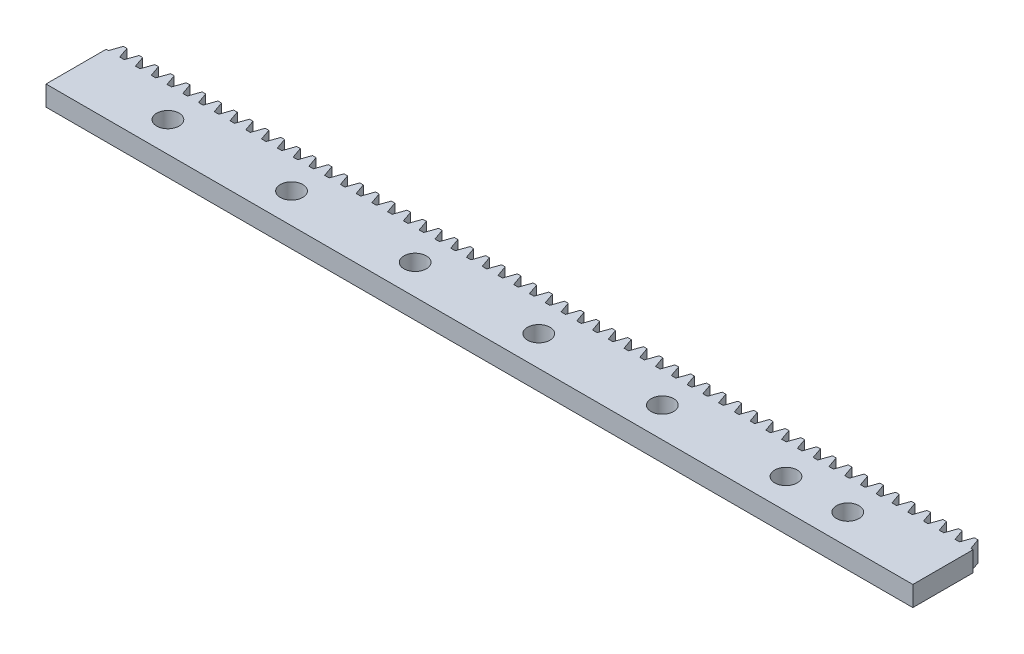
SolidWorks part; units mm, degrees
ref_plane "Front Plane" through (0, 0, 0) normal (0, 0, 1) x (1, 0, 0)
ref_plane "Top Plane" through (0, 0, 0) normal (0, 1, 0) x (1, 0, 0)
ref_plane "Right Plane" through (0, 0, 0) normal (1, 0, 0) x (0, 0, -1)
ref_plane "Plane1" through (0, 0, 0) normal (0, -1, 0) x (1, 0, 0)
sketch "Sketch1" plane through (0, 0, 0) normal (0, -1, 0) x (1, 0, 0)
  line L0 (14.6068, -4.7625) -> (15.3169, -4.7625)
  line L1 (15.3169, -4.7625) -> (15.9263, -6.5115)
  line L2 (15.9263, -6.5115) -> (16.491, -6.5115)
  line L3 (16.491, -6.5115) -> (17.1004, -4.7625)
  line L4 (12.1131, -4.7625) -> (12.8232, -4.7625)
  line L5 (12.8232, -4.7625) -> (13.4327, -6.5115)
  line L6 (13.4327, -6.5115) -> (13.9974, -6.5115)
  line L7 (13.9974, -6.5115) -> (14.6068, -4.7625)
  line L8 (9.6195, -4.7625) -> (10.3296, -4.7625)
  line L9 (10.3296, -4.7625) -> (10.939, -6.5115)
  line L10 (10.939, -6.5115) -> (11.5037, -6.5115)
  line L11 (11.5037, -6.5115) -> (12.1131, -4.7625)
  line L12 (7.1259, -4.7625) -> (7.836, -4.7625)
  line L13 (7.836, -4.7625) -> (8.4454, -6.5115)
  line L14 (8.4454, -6.5115) -> (9.0101, -6.5115)
  line L15 (9.0101, -6.5115) -> (9.6195, -4.7625)
  line L16 (4.6322, -4.7625) -> (5.3423, -4.7625)
  line L17 (5.3423, -4.7625) -> (5.9517, -6.5115)
  line L18 (5.9517, -6.5115) -> (6.5165, -6.5115)
  line L19 (6.5165, -6.5115) -> (7.1259, -4.7625)
  line L20 (2.1386, -4.7625) -> (2.8487, -4.7625)
  line L21 (2.8487, -4.7625) -> (3.4581, -6.5115)
  line L22 (3.4581, -6.5115) -> (4.0228, -6.5115)
  line L23 (4.0228, -6.5115) -> (4.6322, -4.7625)
  line L24 (-0.355, -4.7625) -> (0.355, -4.7625)
  line L25 (0.355, -4.7625) -> (0.9645, -6.5115)
  line L26 (0.9645, -6.5115) -> (1.5292, -6.5115)
  line L27 (1.5292, -6.5115) -> (2.1386, -4.7625)
  line L28 (-2.8487, -4.7625) -> (-2.1386, -4.7625)
  line L29 (-2.1386, -4.7625) -> (-1.5292, -6.5115)
  line L30 (-1.5292, -6.5115) -> (-0.9645, -6.5115)
  line L31 (-0.9645, -6.5115) -> (-0.355, -4.7625)
  line L32 (-5.3423, -4.7625) -> (-4.6322, -4.7625)
  line L33 (-4.6322, -4.7625) -> (-4.0228, -6.5115)
  line L34 (-4.0228, -6.5115) -> (-3.4581, -6.5115)
  line L35 (-3.4581, -6.5115) -> (-2.8487, -4.7625)
  line L36 (-7.836, -4.7625) -> (-7.1259, -4.7625)
  line L37 (-7.1259, -4.7625) -> (-6.5165, -6.5115)
  line L38 (-6.5165, -6.5115) -> (-5.9517, -6.5115)
  line L39 (-5.9517, -6.5115) -> (-5.3423, -4.7625)
  line L40 (-10.3296, -4.7625) -> (-9.6195, -4.7625)
  line L41 (-9.6195, -4.7625) -> (-9.0101, -6.5115)
  line L42 (-9.0101, -6.5115) -> (-8.4454, -6.5115)
  line L43 (-8.4454, -6.5115) -> (-7.836, -4.7625)
  line L44 (-12.8232, -4.7625) -> (-12.1131, -4.7625)
  line L45 (-12.1131, -4.7625) -> (-11.5037, -6.5115)
  line L46 (-11.5037, -6.5115) -> (-10.939, -6.5115)
  line L47 (-10.939, -6.5115) -> (-10.3296, -4.7625)
  line L48 (-15.3169, -4.7625) -> (-14.6068, -4.7625)
  line L49 (-14.6068, -4.7625) -> (-13.9974, -6.5115)
  line L50 (-13.9974, -6.5115) -> (-13.4327, -6.5115)
  line L51 (-13.4327, -6.5115) -> (-12.8232, -4.7625)
  line L52 (-17.8105, -4.7625) -> (-17.1004, -4.7625)
  line L53 (-17.1004, -4.7625) -> (-16.491, -6.5115)
  line L54 (-16.491, -6.5115) -> (-15.9263, -6.5115)
  line L55 (-15.9263, -6.5115) -> (-15.3169, -4.7625)
  line L56 (-20.3042, -4.7625) -> (-19.5941, -4.7625)
  line L57 (-19.5941, -4.7625) -> (-18.9846, -6.5115)
  line L58 (-18.9846, -6.5115) -> (-18.4199, -6.5115)
  line L59 (-18.4199, -6.5115) -> (-17.8105, -4.7625)
  line L60 (-22.7978, -4.7625) -> (-22.0877, -4.7625)
  line L61 (-22.0877, -4.7625) -> (-21.4783, -6.5115)
  line L62 (-21.4783, -6.5115) -> (-20.9136, -6.5115)
  line L63 (-20.9136, -6.5115) -> (-20.3042, -4.7625)
  line L64 (-25.2914, -4.7625) -> (-24.5813, -4.7625)
  line L65 (-24.5813, -4.7625) -> (-23.9719, -6.5115)
  line L66 (-23.9719, -6.5115) -> (-23.4072, -6.5115)
  line L67 (-23.4072, -6.5115) -> (-22.7978, -4.7625)
  line L68 (-27.7851, -4.7625) -> (-27.075, -4.7625)
  line L69 (-27.075, -4.7625) -> (-26.4656, -6.5115)
  line L70 (-26.4656, -6.5115) -> (-25.9009, -6.5115)
  line L71 (-25.9009, -6.5115) -> (-25.2914, -4.7625)
  line L72 (-30.2787, -4.7625) -> (-29.5686, -4.7625)
  line L73 (-29.5686, -4.7625) -> (-28.9592, -6.5115)
  line L74 (-28.9592, -6.5115) -> (-28.3945, -6.5115)
  line L75 (-28.3945, -6.5115) -> (-27.7851, -4.7625)
  line L76 (-32.7724, -4.7625) -> (-32.0623, -4.7625)
  line L77 (-32.0623, -4.7625) -> (-31.4528, -6.5115)
  line L78 (-31.4528, -6.5115) -> (-30.8881, -6.5115)
  line L79 (-30.8881, -6.5115) -> (-30.2787, -4.7625)
  line L80 (-35.266, -4.7625) -> (-34.5559, -4.7625)
  line L81 (-34.5559, -4.7625) -> (-33.9465, -6.5115)
  line L82 (-33.9465, -6.5115) -> (-33.3818, -6.5115)
  line L83 (-33.3818, -6.5115) -> (-32.7724, -4.7625)
  line L84 (-37.7596, -4.7625) -> (-37.0495, -4.7625)
  line L85 (-37.0495, -4.7625) -> (-36.4401, -6.5115)
  line L86 (-36.4401, -6.5115) -> (-35.8754, -6.5115)
  line L87 (-35.8754, -6.5115) -> (-35.266, -4.7625)
  line L88 (-40.2533, -4.7625) -> (-39.5432, -4.7625)
  line L89 (-39.5432, -4.7625) -> (-38.9338, -6.5115)
  line L90 (-38.9338, -6.5115) -> (-38.3691, -6.5115)
  line L91 (-38.3691, -6.5115) -> (-37.7596, -4.7625)
  line L92 (-42.7469, -4.7625) -> (-42.0368, -4.7625)
  line L93 (-42.0368, -4.7625) -> (-41.4274, -6.5115)
  line L94 (-41.4274, -6.5115) -> (-40.8627, -6.5115)
  line L95 (-40.8627, -6.5115) -> (-40.2533, -4.7625)
  line L96 (-45.2406, -4.7625) -> (-44.5305, -4.7625)
  line L97 (-44.5305, -4.7625) -> (-43.921, -6.5115)
  line L98 (-43.921, -6.5115) -> (-43.3563, -6.5115)
  line L99 (-43.3563, -6.5115) -> (-42.7469, -4.7625)
  line L100 (-47.7342, -4.7625) -> (-47.0241, -4.7625)
  line L101 (-47.0241, -4.7625) -> (-46.4147, -6.5115)
  line L102 (-46.4147, -6.5115) -> (-45.85, -6.5115)
  line L103 (-45.85, -6.5115) -> (-45.2406, -4.7625)
  line L104 (-50.2278, -4.7625) -> (-49.5177, -4.7625)
  line L105 (-49.5177, -4.7625) -> (-48.9083, -6.5115)
  line L106 (-48.9083, -6.5115) -> (-48.3436, -6.5115)
  line L107 (-48.3436, -6.5115) -> (-47.7342, -4.7625)
  line L108 (-52.7215, -4.7625) -> (-52.0114, -4.7625)
  line L109 (-52.0114, -4.7625) -> (-51.402, -6.5115)
  line L110 (-51.402, -6.5115) -> (-50.8372, -6.5115)
  line L111 (-50.8372, -6.5115) -> (-50.2278, -4.7625)
  line L112 (-55.2151, -4.7625) -> (-54.505, -4.7625)
  line L113 (-54.505, -4.7625) -> (-53.8956, -6.5115)
  line L114 (-53.8956, -6.5115) -> (-53.3309, -6.5115)
  line L115 (-53.3309, -6.5115) -> (-52.7215, -4.7625)
  line L116 (-57.7087, -4.7625) -> (-56.9987, -4.7625)
  line L117 (-56.9987, -4.7625) -> (-56.3892, -6.5115)
  line L118 (-56.3892, -6.5115) -> (-55.8245, -6.5115)
  line L119 (-55.8245, -6.5115) -> (-55.2151, -4.7625)
  line L120 (-60.2024, -4.7625) -> (-59.4923, -4.7625)
  line L121 (-59.4923, -4.7625) -> (-58.8829, -6.5115)
  line L122 (-58.8829, -6.5115) -> (-58.3182, -6.5115)
  line L123 (-58.3182, -6.5115) -> (-57.7087, -4.7625)
  line L124 (-62.696, -4.7625) -> (-61.9859, -4.7625)
  line L125 (-61.9859, -4.7625) -> (-61.3765, -6.5115)
  line L126 (-61.3765, -6.5115) -> (-60.8118, -6.5115)
  line L127 (-60.8118, -6.5115) -> (-60.2024, -4.7625)
  line L128 (-65.1897, -4.7625) -> (-64.4796, -4.7625)
  line L129 (-64.4796, -4.7625) -> (-63.8702, -6.5115)
  line L130 (-63.8702, -6.5115) -> (-63.3054, -6.5115)
  line L131 (-63.3054, -6.5115) -> (-62.696, -4.7625)
  line L132 (-67.6833, -4.7625) -> (-66.9732, -4.7625)
  line L133 (-66.9732, -4.7625) -> (-66.3638, -6.5115)
  line L134 (-66.3638, -6.5115) -> (-65.7991, -6.5115)
  line L135 (-65.7991, -6.5115) -> (-65.1897, -4.7625)
  line L136 (-70.1769, -4.7625) -> (-69.4668, -4.7625)
  line L137 (-69.4668, -4.7625) -> (-68.8574, -6.5115)
  line L138 (-68.8574, -6.5115) -> (-68.2927, -6.5115)
  line L139 (-68.2927, -6.5115) -> (-67.6833, -4.7625)
  line L140 (-72.6706, -4.7625) -> (-71.9605, -4.7625)
  line L141 (-71.9605, -4.7625) -> (-71.3511, -6.5115)
  line L142 (-71.3511, -6.5115) -> (-70.7864, -6.5115)
  line L143 (-70.7864, -6.5115) -> (-70.1769, -4.7625)
  line L144 (-75.1642, -4.7625) -> (-74.4541, -4.7625)
  line L145 (-74.4541, -4.7625) -> (-73.8447, -6.5115)
  line L146 (-73.8447, -6.5115) -> (-73.28, -6.5115)
  line L147 (-73.28, -6.5115) -> (-72.6706, -4.7625)
  line L148 (-77.6579, -4.7625) -> (-76.9478, -4.7625)
  line L149 (-76.9478, -4.7625) -> (-76.3383, -6.5115)
  line L150 (-76.3383, -6.5115) -> (-75.7736, -6.5115)
  line L151 (-75.7736, -6.5115) -> (-75.1642, -4.7625)
  line L152 (-80.1515, -4.7625) -> (-79.4414, -4.7625)
  line L153 (-79.4414, -4.7625) -> (-78.832, -6.5115)
  line L154 (-78.832, -6.5115) -> (-78.2673, -6.5115)
  line L155 (-78.2673, -6.5115) -> (-77.6579, -4.7625)
  line L156 (-82.6451, -4.7625) -> (-81.935, -4.7625)
  line L157 (-81.935, -4.7625) -> (-81.3256, -6.5115)
  line L158 (-81.3256, -6.5115) -> (-80.7609, -6.5115)
  line L159 (-80.7609, -6.5115) -> (-80.1515, -4.7625)
  line L160 (-85.1388, -4.7625) -> (-84.4287, -4.7625)
  line L161 (-84.4287, -4.7625) -> (-83.8193, -6.5115)
  line L162 (-83.8193, -6.5115) -> (-83.2546, -6.5115)
  line L163 (-83.2546, -6.5115) -> (-82.6451, -4.7625)
  line L164 (-87.6324, -4.7625) -> (-86.9223, -4.7625)
  line L165 (-86.9223, -4.7625) -> (-86.3129, -6.5115)
  line L166 (-86.3129, -6.5115) -> (-85.7482, -6.5115)
  line L167 (-85.7482, -6.5115) -> (-85.1388, -4.7625)
  line L168 (-90.1261, -4.7625) -> (-89.416, -4.7625)
  line L169 (-89.416, -4.7625) -> (-88.8065, -6.5115)
  line L170 (-88.8065, -6.5115) -> (-88.2418, -6.5115)
  line L171 (-88.2418, -6.5115) -> (-87.6324, -4.7625)
  line L172 (-92.6197, -4.7625) -> (-91.9096, -4.7625)
  line L173 (-91.9096, -4.7625) -> (-91.3002, -6.5115)
  line L174 (-91.3002, -6.5115) -> (-90.7355, -6.5115)
  line L175 (-90.7355, -6.5115) -> (-90.1261, -4.7625)
  line L176 (-95.1133, -4.7625) -> (-94.4032, -4.7625)
  line L177 (-94.4032, -4.7625) -> (-93.7938, -6.5115)
  line L178 (-93.7938, -6.5115) -> (-93.2291, -6.5115)
  line L179 (-93.2291, -6.5115) -> (-92.6197, -4.7625)
  line L180 (-97.607, -4.7625) -> (-96.8969, -4.7625)
  line L181 (-96.8969, -4.7625) -> (-96.2875, -6.5115)
  line L182 (-96.2875, -6.5115) -> (-95.7228, -6.5115)
  line L183 (-95.7228, -6.5115) -> (-95.1133, -4.7625)
  line L184 (-100.1006, -4.7625) -> (-99.3905, -4.7625)
  line L185 (-99.3905, -4.7625) -> (-98.7811, -6.5115)
  line L186 (-98.7811, -6.5115) -> (-98.2164, -6.5115)
  line L187 (-98.2164, -6.5115) -> (-97.607, -4.7625)
  line L188 (-102.5943, -4.7625) -> (-101.8842, -4.7625)
  line L189 (-101.8842, -4.7625) -> (-101.2747, -6.5115)
  line L190 (-101.2747, -6.5115) -> (-100.71, -6.5115)
  line L191 (-100.71, -6.5115) -> (-100.1006, -4.7625)
  line L192 (-105.0879, -4.7625) -> (-104.3778, -4.7625)
  line L193 (-104.3778, -4.7625) -> (-103.7684, -6.5115)
  line L194 (-103.7684, -6.5115) -> (-103.2037, -6.5115)
  line L195 (-103.2037, -6.5115) -> (-102.5943, -4.7625)
  line L196 (-107.5815, -4.7625) -> (-106.8714, -4.7625)
  line L197 (-106.8714, -4.7625) -> (-106.262, -6.5115)
  line L198 (-106.262, -6.5115) -> (-105.6973, -6.5115)
  line L199 (-105.6973, -6.5115) -> (-105.0879, -4.7625)
  line L200 (-110.0752, -4.7625) -> (-109.3651, -4.7625)
  line L201 (-109.3651, -4.7625) -> (-108.7557, -6.5115)
  line L202 (-108.7557, -6.5115) -> (-108.1909, -6.5115)
  line L203 (-108.1909, -6.5115) -> (-107.5815, -4.7625)
  line L204 (-112.5688, -4.7625) -> (-111.8587, -4.7625)
  line L205 (-111.8587, -4.7625) -> (-111.2493, -6.5115)
  line L206 (-111.2493, -6.5115) -> (-110.6846, -6.5115)
  line L207 (-110.6846, -6.5115) -> (-110.0752, -4.7625)
  line L208 (-115.0624, -4.7625) -> (-114.3524, -4.7625)
  line L209 (-114.3524, -4.7625) -> (-113.7429, -6.5115)
  line L210 (-113.7429, -6.5115) -> (-113.1782, -6.5115)
  line L211 (-113.1782, -6.5115) -> (-112.5688, -4.7625)
  line L212 (-117.2035, -4.7625) -> (-116.846, -4.7625)
  line L213 (-116.846, -4.7625) -> (-116.2366, -6.5115)
  line L214 (-116.2366, -6.5115) -> (-115.6719, -6.5115)
  line L215 (-115.6719, -6.5115) -> (-115.0624, -4.7625)
  line L256 (17.1004, -4.7625) -> (17.8105, -4.7625)
  line L257 (17.8105, -4.7625) -> (18.4199, -6.5115)
  line L258 (18.4199, -6.5115) -> (18.9846, -6.5115)
  line L259 (18.9846, -6.5115) -> (19.5941, -4.7625)
  line L260 (19.5941, -4.7625) -> (19.9491, -4.7625)
  line L261 (-117.2035, -4.7625) -> (-117.2035, 4.7625)
  line L457 (19.9491, 4.7625) -> (-117.2035, 4.7625)
  line L458 (19.9491, -4.7625) -> (19.9491, 4.7625)
  circle A0 centre (4.887, 0) radius 1.778
  circle A8 centre (-102.677, 0) radius 1.778
  circle A9 centre (-83.119, 0) radius 1.778
  circle A10 centre (-63.561, 0) radius 1.778
  circle A11 centre (-44.003, 0) radius 1.778
  circle A12 centre (-24.445, 0) radius 1.778
  circle A13 centre (-4.887, 0) radius 1.778
  dimension "D1" = 0.5647
  dimension "D2" = 0.7101
  dimension "D4" = 1.8842
  dimension "D6" = 1.749
  dimension "D7" = 109.21
  dimension "D8" = 4.7625
  dimension "D9" = 14.7071
  dimension "D10" = 2.4936
  dimension "D3" = 55
extrude "Boss-Extrude1" add sketch "Sketch1" against normal blind 3.175
